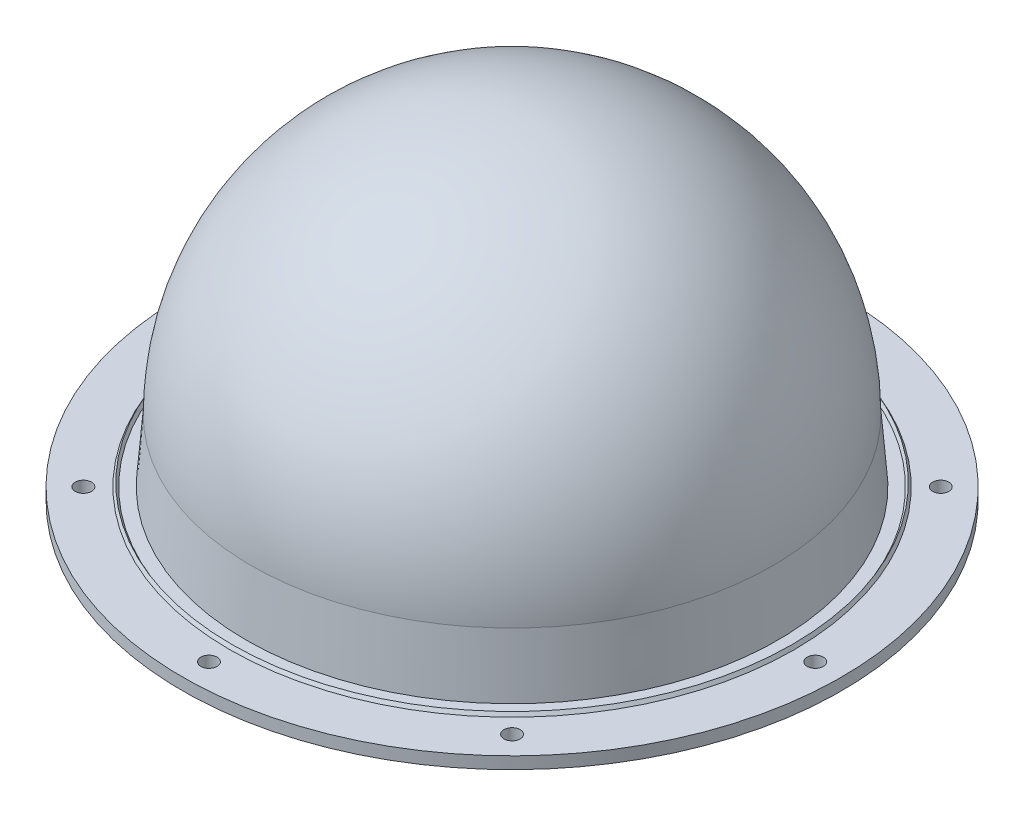
SolidWorks part; units mm, degrees
material "PC 高粘度"
ref_plane "前视基准面" through (0, 0, 0) normal (0, 0, 1) x (1, 0, 0)
ref_plane "上视基准面" through (0, 0, 0) normal (0, 1, 0) x (1, 0, 0)
ref_plane "右视基准面" through (0, 0, 0) normal (1, 0, 0) x (0, 0, -1)
other "Configuration Table"
sketch "草图1" plane through (0, 0, 0) normal (0, 0, 1) x (1, 0, 0)
  line L0 (0, 0) -> (0, 95) construction
  line L1 (-73.1, 0) -> (-71.4295, 21)
  line L2 (-71.4295, 21) -> (-74, 21)
  line L3 (-74, 21) -> (-75.4, 3.4)
  line L4 (-75.4, 3.4) -> (-93.5, 3.4)
  line L5 (-93.5, 3.4) -> (-93.5, 0)
  line L6 (-93.5, 0) -> (-73.1, 0)
  line L7 (-71.4295, 21) -> (0, 21) construction
  line L8 (-73.1, 0) -> (0, 0) construction
  line L9 (0, 92.4295) -> (0, 95)
  line L10 (-80.0774, 3.4) -> (-79.5, 4.4)
  line L11 (-79.5, 4.4) -> (-78.9226, 3.4)
  line L12 (-78.9226, 3.4) -> (-80.0774, 3.4)
  arc A0 (0, 95) -> (-74, 21) centre (0, 21) ccw
  arc A1 (0, 92.4295) -> (-71.4295, 21) centre (0, 21) ccw
  dimension "D1" = 95
  dimension "D2" = 150.8
  dimension "D3" = 21
  dimension "D4" = 187
  dimension "D5" = 146.2
  dimension "D6" = 3.4
  dimension "D7" = 1
  dimension "D8" = 60
  dimension "D9" = 60
  dimension "D10" = 159
revolve "旋转1" add sketch "草图1" angle 360 about L0
sketch "草图2" plane through (0, 3.4, 0) normal (0, 1, 0) x (1, 0, 0)
  circle A0 centre (0, 0) radius 86
  circle A1 centre (0, 86) radius 2.3
  dimension "D1" = 172
  dimension "D2" = 4.6
extrude "切除-拉伸1" cut sketch "草图2" against normal blind 10 contours A0 A1 | A0 A1
pattern_circular "阵列(圆周)1" count 8 over 360 about axis through (0, 0, 0) along (0, 1, 0) of "切除-拉伸1"
